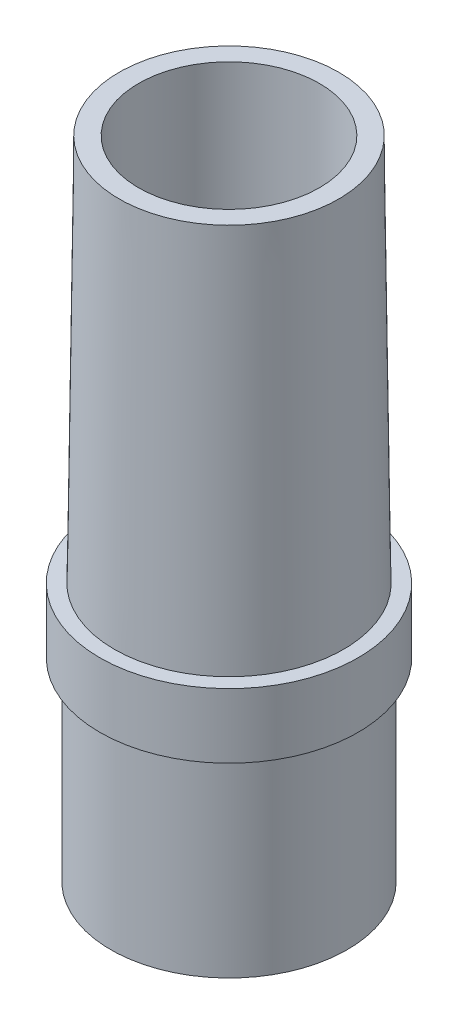
SolidWorks part; units mm, degrees
ref_plane "Спереди" through (0, 0, 0) normal (0, 0, 1) x (1, 0, 0)
ref_plane "Сверху" through (0, 0, 0) normal (0, 1, 0) x (1, 0, 0)
ref_plane "Справа" through (0, 0, 0) normal (1, 0, 0) x (0, 0, -1)
sketch "Эскиз1" plane through (0, 0, 0) normal (0, 1, 0) x (1, 0, 0)
  circle A0 centre (0, 0) radius 20
extrude "Вытянуть-Тонкостенный1" add sketch "Эскиз1" along normal blind 100 thin thin type one direction reverse wall 6
sketch "Эскиз2" plane through (0, 0, 0) normal (1, 0, 0) x (0, 0, -1)
  line L0 (-20, 0) -> (20, 0) construction
  line L1 (18.3, 30) -> (20, 30)
  line L2 (18.3, 30) -> (18.3, 0)
  line L3 (18.3, 0) -> (20, 0)
  line L4 (20, 30) -> (20, 0)
  line L5 (20, 0) -> (20, 100) construction
  line L6 (17, 100) -> (17.75, 40.0016)
  line L7 (20, 100) -> (-20, 100) construction
  line L8 (17.75, 40.0016) -> (20, 40.0016)
  line L9 (20, 40.0016) -> (20, 100)
  line L10 (20, 100) -> (17, 100)
  line L11 (0, -5.8551) -> (0, 103.5862) construction
  point P12 (0, 0)
revolve "Вырез-Повернуть1" cut sketch "Эскиз2" angle 360 about L11
